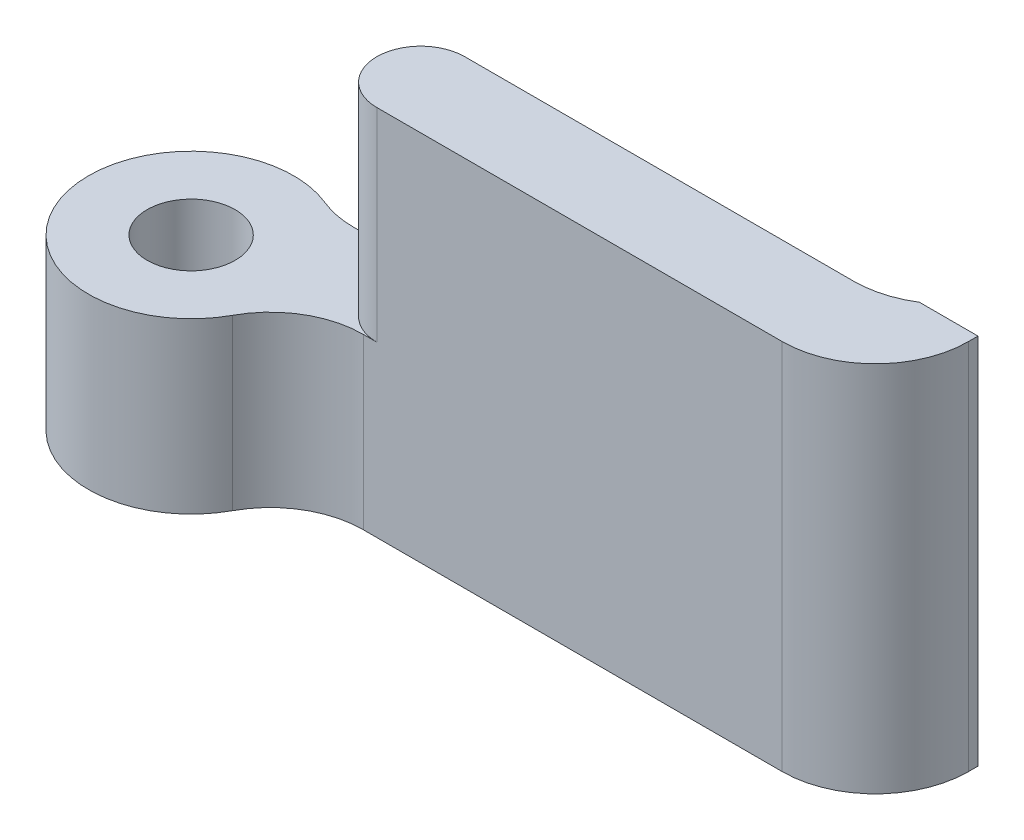
SolidWorks part; units mm, degrees
ref_plane "Front Plane" through (0, 0, 0) normal (0, 0, 1) x (1, 0, 0)
ref_plane "Top Plane" through (0, 0, 0) normal (0, 1, 0) x (1, 0, 0)
ref_plane "Right Plane" through (0, 0, 0) normal (1, 0, 0) x (0, 0, -1)
sketch "Sketch1" plane through (0, 0, 0) normal (0, 1, 0) x (1, 0, 0)
  line L0 (-18.5638, 11.2355) -> (1.2664, 11.2355)
  line L1 (1.2664, 11.2355) -> (1.2664, 14.2355)
  line L2 (1.2664, 14.2355) -> (-20.261, 14.2355)
  line L5 (50.6802, -59.5018) -> (50.6802, -56.5018) construction
  line L6 (27.35, -59.5018) -> (50.6802, -59.5018) construction
  circle A0 centre (-22.0638, 11.2355) radius 3.5
  dimension "D1" = 7
  dimension "D2" = 3
  dimension "D3" = 1
extrude "Boss-Extrude1" add sketch "Sketch1" along normal blind 12.7
sketch "Sketch2" plane through (0, 12.7, 0) normal (0, 1, 0) x (1, 0, 0)
  line L0 (-18.5638, 11.2355) -> (1.2664, 11.2355) construction
  line L1 (1.2664, 14.2355) -> (-20.261, 14.2355) construction
  line L2 (-15.7336, 11.2355) -> (-15.7336, 14.2355) construction
  line L3 (1.2664, 11.2355) -> (1.2664, 14.2355) construction
  line L4 (-15.7336, 11.2355) -> (-15.7336, 4.0688)
  line L5 (-15.7336, 4.0688) -> (-31.2061, 4.0688)
  line L6 (-31.2061, 4.0688) -> (-31.2061, 17.9688)
  line L7 (-31.2061, 17.9688) -> (-15.7336, 17.9688)
  line L8 (-15.7336, 17.9688) -> (-15.7336, 14.2355)
  arc A0 (-15.7336, 11.2355) -> (-15.7336, 14.2355) centre (-15.7336, 12.7355) cw
  dimension "D1" = 17
extrude "Cut-Extrude1" cut sketch "Sketch2" against normal up to surface (6.93 mm away)
sketch "Sketch3" plane through (0, 5.77, 0) normal (0, 1, 0) x (1, 0, 0)
  circle A0 centre (-22.0638, 11.2355) radius 1.5
  arc A1 (-20.261, 14.2355) -> (-18.5638, 11.2355) centre (-22.0638, 11.2355) ccw construction
  dimension "D1" = 3
extrude "Cut-Extrude2" cut sketch "Sketch3" against normal through all
sketch "Sketch4" plane through (0, 12.7, 0) normal (0, 1, 0) x (1, 0, 0)
  line L0 (1.2664, 14.2355) -> (1.2664, 14.7355)
  line L1 (1.2664, 14.7355) -> (-0.7336, 14.7355)
  line L2 (-0.7336, 14.7355) -> (-0.7336, 14.2355)
  line L3 (1.2664, 14.2355) -> (-15.7336, 14.2355) construction
  line L4 (-0.7336, 14.2355) -> (1.2664, 14.2355)
  arc A0 (-0.7336, 14.7355) -> (-2.4728, 14.2355) centre (-2.4728, 17.5105) cw
  line M4 (1.2664, 14.2355) -> (-15.7336, 14.2355)
  dimension "D3" = 3.275
  dimension "D1" = 0.5
  dimension "D2" = 2
extrude "Boss-Extrude2" add sketch "Sketch4" against normal up to surface (12.7 mm away) contours L1 L2 L0 M4 | L2 A0 M4 up to face at (-22.0638, 0, -9.7355)
fillet "Fillet1" radius 3.175 3 edges at (1.2664, 6.35, -11.2355) (-20.261, 2.885, -14.2355) (-18.5638, 2.885, -11.2355)
sketch "Sketch5" plane through (0, 0, -14.2355) normal (0, 0, -1) x (-1, 0, 0)
  circle A0 centre (-37.2215, -42.8314) radius 2
  circle A1 centre (-37.2215, -47.5314) radius 2
  dimension "D1" = 4
extrude "Cut-Extrude3" cut sketch "Sketch5" against normal blind 10
sketch "Sketch6" plane through (0, 0, -14.2355) normal (0, 0, -1) x (-1, 0, 0)
  circle A0 centre (4.7336, 6.35) radius 1.585
  circle A1 centre (-44.6802, -45.1814) radius 1.585 construction
extrude "Cut-Extrude4" cut sketch "Sketch6" against normal blind 1.5
